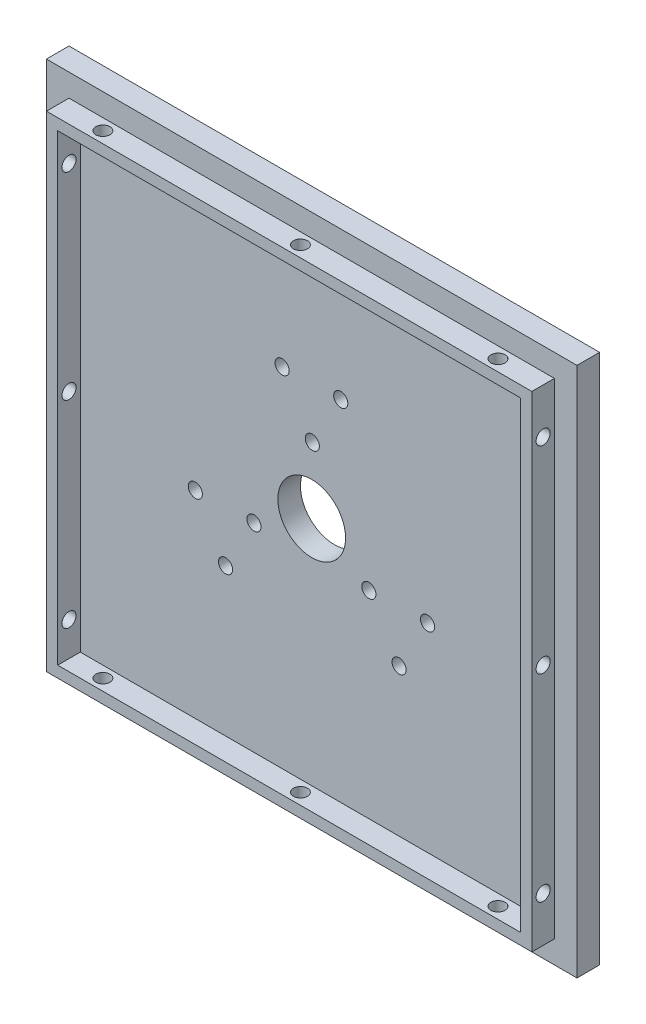
SolidWorks part; units mm, degrees
ref_plane "前视基准面" through (0, 0, 0) normal (0, 0, 1) x (1, 0, 0)
ref_plane "上视基准面" through (0, 0, 0) normal (0, 1, 0) x (1, 0, 0)
ref_plane "右视基准面" through (0, 0, 0) normal (1, 0, 0) x (0, 0, -1)
sketch "草图1" plane through (0, 0, 0) normal (0, 0, 1) x (1, 0, 0)
  line L0 (0, 0) -> (47, 0) construction
  line L1 (0, 0) -> (-47, 0) construction
  line L2 (0, 0) -> (0, 47) construction
  line L3 (0, 0) -> (0, -47) construction
  line L4 (0, 47) -> (47, 47)
  line L5 (0, -47) -> (-47, -47)
  line L6 (0, -47) -> (47, -47)
  line L7 (-47, 47) -> (-47, 0)
  line L8 (-47, 47) -> (0, 47)
  line L9 (-47, 0) -> (-47, -47)
  line L10 (47, -47) -> (47, 0)
  line L11 (47, 0) -> (47, 47)
  circle A0 centre (-5.2477, 20.6579) radius 1.25
  circle A1 centre (5.143, 20.8392) radius 1.25
  circle A2 centre (0, 0) radius 6
  circle A3 centre (0.1047, 11.7499) radius 1.25
  circle A4 centre (20.5141, -5.7843) radius 1.25
  circle A5 centre (15.4758, -14.8736) radius 1.25
  circle A6 centre (10.1234, -5.9656) radius 1.25
  circle A11 centre (-15.2664, -14.8736) radius 1.25
  circle A12 centre (-20.6188, -5.9656) radius 1.25
  circle A13 centre (-10.2281, -5.7843) radius 1.25
  point P24 (0, 0)
  point P25 (0, 0)
  point P26 (-47.9772, 0)
  point P27 (0, 0)
  point P28 (0, 16.75)
  point P29 (0, 16.75)
  point P30 (0, 0)
  point P31 (0, 0)
  point P33 (0, 16.75)
  point P44 (0, 0)
  dimension "D1" = 3
extrude "凸台-拉伸1" add sketch "草图1" along normal blind 4 contours L10 L11 L4 L8 L7 L9 L5 L6 A13 A12 A11 A6 A5 A4 A2
sketch "草图3" plane through (0, 0, 0) normal (0, 1, 0) x (1, 0, 0)
  line L0 (-43, -4) -> (-41, -4)
  line L1 (-41, -4) -> (-41, -8)
  line L2 (-41, -8) -> (-43, -8)
  line L3 (-43, -8) -> (-43, -4)
  line L4 (0, -4) -> (0, -9.8071) construction
  line L5 (43, -8) -> (43, -4)
  line L6 (41, -8) -> (43, -8)
  line L7 (41, -4) -> (41, -8)
  line L8 (43, -4) -> (41, -4)
extrude "凸台-拉伸2" add sketch "草图3" along normal mid plane 86
sketch "草图4" plane through (0, 0, 0) normal (1, 0, 0) x (0, 0, -1)
  line L0 (-4, -43) -> (-8, -43)
  line L1 (-8, -43) -> (-8, -41)
  line L2 (-8, -41) -> (-4, -41)
  line L3 (-4, -41) -> (-4, -43)
  line L9 (-4, 43) -> (-8, 43)
  line L10 (-8, 43) -> (-8, 41)
  line L11 (-8, 41) -> (-4, 41)
  line L12 (-4, 41) -> (-4, 43)
extrude "凸台-拉伸3" add sketch "草图4" along normal mid plane 86
ref_plane "基准面2" through (0, 43, 0) normal (0, 1, 0) x (1, 0, 0)
sketch "草图5" plane through (0, 43, 0) normal (0, 1, 0) x (1, 0, 0)
  circle A0 centre (0, -6) radius 1.25
  circle A1 centre (35, -6) radius 1.25
  circle A2 centre (-35, -6) radius 1.25
  dimension "D1" = 2
  dimension "D2" = 2
extrude "切除-拉伸1" cut sketch "草图5" against normal blind 2
pattern_circular "阵列(圆周)1" count 4 every 90 about axis through (0, 0, 4) along (0, 0, 1) of "切除-拉伸1"
